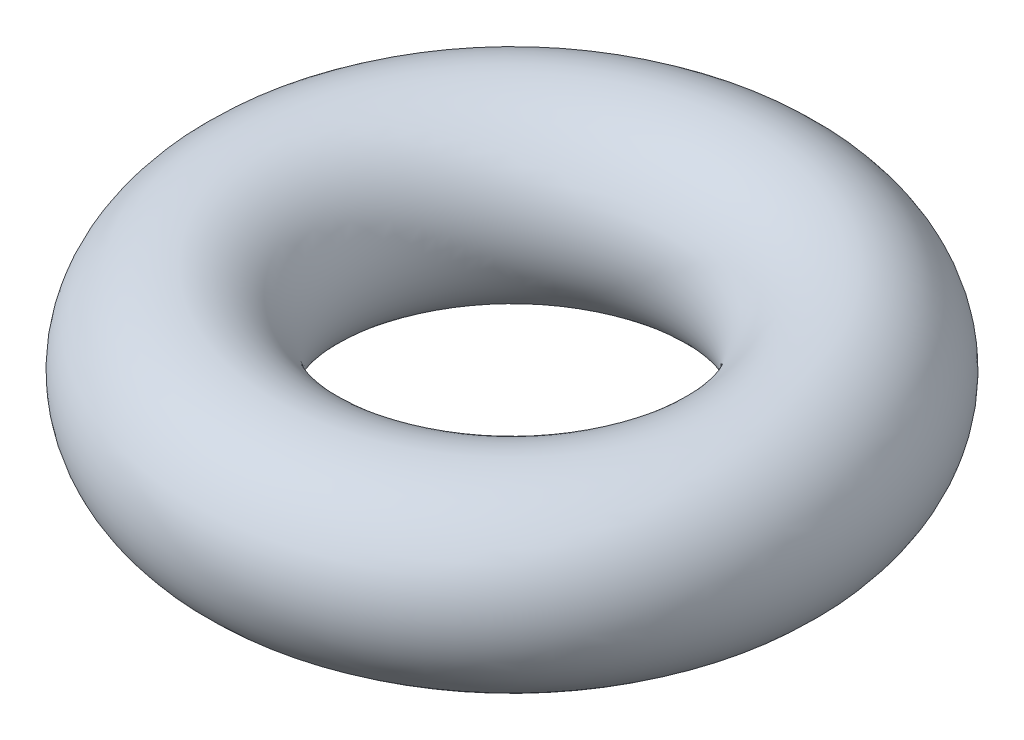
SolidWorks part; units mm, degrees
ref_plane "前视基准面" through (0, 0, 0) normal (0, 0, 1) x (1, 0, 0)
ref_plane "上视基准面" through (0, 0, 0) normal (0, 1, 0) x (1, 0, 0)
ref_plane "右视基准面" through (0, 0, 0) normal (1, 0, 0) x (0, 0, -1)
sketch "草图1" plane through (0, 0, 0) normal (0, 0, 1) x (1, 0, 0)
  circle A0 centre (0, 0) radius 11.769
sketch "草图2" plane through (0, 0, 0) normal (0, 1, 0) x (1, 0, 0)
  circle A0 centre (30.8833, 0) radius 30.8833
sweep "扫描1" add profiles "草图1" path "草图2"
